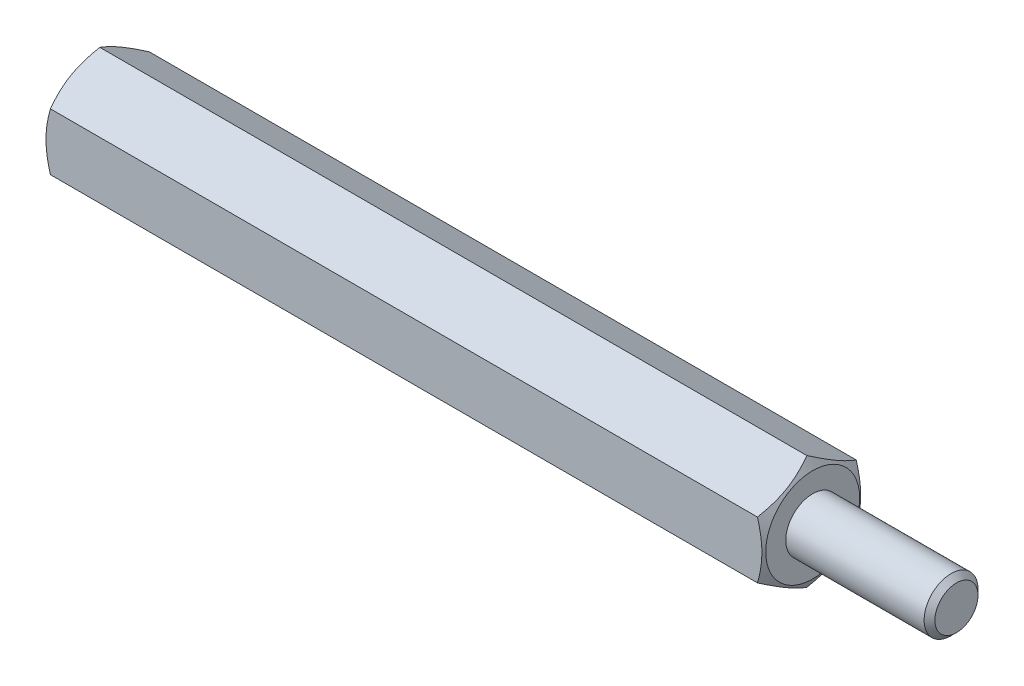
SolidWorks part; units mm, degrees
material "Brass"
ref_plane "Front Plane" through (0, 0, 0) normal (0, 0, 1) x (1, 0, 0)
ref_plane "Top Plane" through (0, 0, 0) normal (0, 1, 0) x (1, 0, 0)
ref_plane "Right Plane" through (0, 0, 0) normal (1, 0, 0) x (0, 0, -1)
sketch "Sketch1" plane through (0, 0, 0) normal (1, 0, 0) x (0, 0, -1)
  line L1 (0, 3.1754) -> (-2.75, 1.5877)
  line L2 (-2.75, 1.5877) -> (-2.75, -1.5877)
  line L3 (-2.75, -1.5877) -> (0, -3.1754)
  line L4 (0, -3.1754) -> (2.75, -1.5877)
  line L5 (2.75, -1.5877) -> (2.75, 1.5877)
  line L6 (2.75, 1.5877) -> (0, 3.1754)
  circle A0 centre (0, 0) radius 2.75 construction
extrude "Boss-Extrude1" add sketch "Sketch1" along normal blind 40
sketch "Sketch2" plane through (40, 0, 0) normal (1, 0, 0) x (0, 0, -1)
  circle A0 centre (0, 0) radius 1.5
extrude "Boss-Extrude2" add sketch "Sketch2" along normal blind 8
sketch "Sketch3" plane through (0, 0, 0) normal (-1, 0, 0) x (0, 0, 1)
  circle A0 centre (0, 0) radius 1.5
extrude "Cut-Extrude1" cut sketch "Sketch3" against normal blind 10
sketch "Sketch4" plane through (0, 0, 0) normal (0, 1, 0) x (1, 0, 0)
  line L0 (0, 0) -> (0, 2.6125)
  line L1 (0, 2.6125) -> (4.3921, 10.2198)
  line L2 (0, 2.6125) -> (0, 10.2198)
  line L3 (0, 10.2198) -> (4.3921, 10.2198)
  line L4 (0, 0) -> (-8.2035, 0) construction
  line L5 (40, 0) -> (40, 2.6125)
  line L6 (40, 2.6125) -> (35.6079, 10.2198)
  line L7 (40, 2.6125) -> (40, 10.2198)
  line L8 (40, 10.2198) -> (35.6079, 10.2198)
  line L9 (0, 0) -> (40, 0)
  dimension "D1" = 40
revolve "Cut-Revolve1" cut sketch "Sketch4" angle 360 about L4
chamfer "Chamfer1" distance 0.3 angle 45 1 edges at (48, 0, -1.5)
